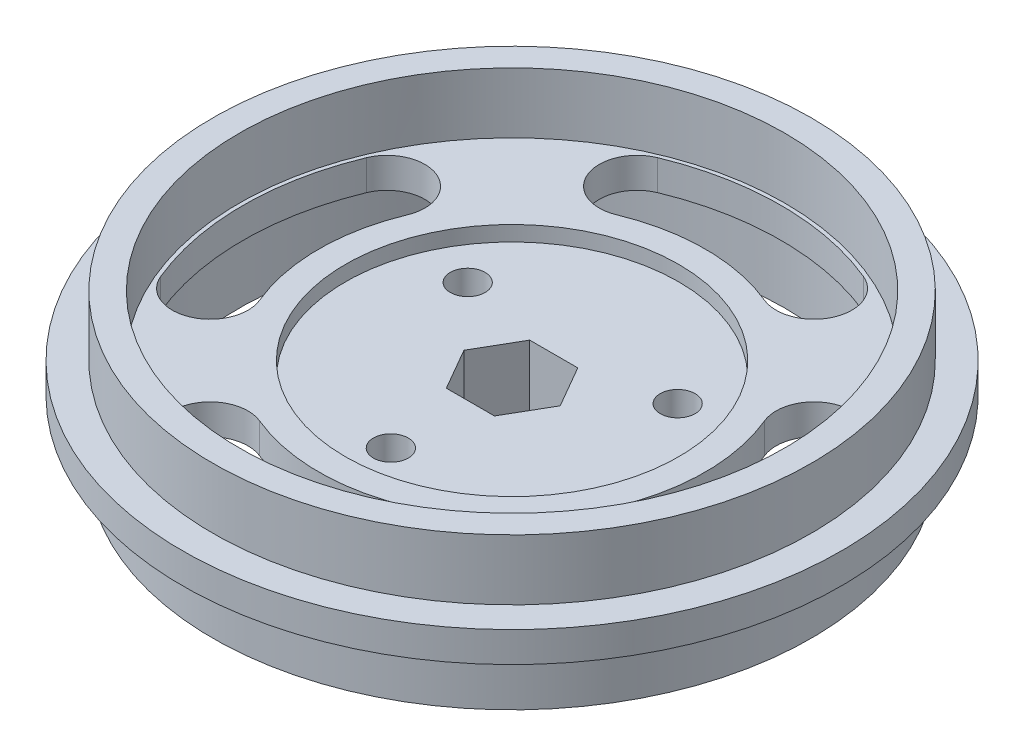
SolidWorks part; units mm, degrees
ref_plane "Ön Düzlem" through (0, 0, 0) normal (0, 0, 1) x (1, 0, 0)
ref_plane "Üst Düzlem" through (0, 0, 0) normal (0, 1, 0) x (1, 0, 0)
ref_plane "Sağ Düzlem" through (0, 0, 0) normal (1, 0, 0) x (0, 0, -1)
sketch "Sketch1" plane through (0, 0, 0) normal (0, 0, 1) x (1, 0, 0)
  line L0 (18, 5) -> (18, -5)
  line L1 (18, 5) -> (19.75, 5)
  line L2 (19.75, 5) -> (19.75, 1)
  line L3 (19.75, 1) -> (21.75, 1)
  line L4 (21.75, 1) -> (21.75, -1)
  line L5 (21.75, -1) -> (19.75, -1)
  line L6 (19.75, -1) -> (19.75, -5)
  line L7 (19.75, -5) -> (18, -5)
  line L8 (0, 0) -> (0, 50000) construction
  point P2 (18, 0)
  point P4 (21.75, 0)
  dimension "D1" = 18
  dimension "D2" = 10
  dimension "D3" = 2
  dimension "D4" = 4
  dimension "D5" = 1.75
  dimension "D6" = 2
revolve "Revolve1" add sketch "Sketch1" angle 360 about L8
ref_plane "Plane1" through (0, 0, 0) normal (0, 1, 0) x (1, 0, 0)
sketch "Sketch3" plane through (0, 0, 0) normal (0, 1, 0) x (1, 0, 0)
  line L0 (-6.7926, 16.3989) -> (0, 0) construction
  line L1 (0, 0) -> (6.7926, 16.3989) construction
  circle A0 centre (0, 0) radius 18
  circle A1 centre (0, 0) radius 18 construction
  arc A2 (-6.7926, 16.3989) -> (6.7926, 16.3989) centre (0, 0) cw
  arc A3 (4.8792, 11.7795) -> (-4.8792, 11.7795) centre (0, 0) ccw
  arc A4 (-6.7926, 16.3989) -> (-4.8792, 11.7795) centre (-5.8359, 14.0892) ccw
  arc A5 (4.8792, 11.7795) -> (6.7926, 16.3989) centre (5.8359, 14.0892) ccw
  arc A6 (11.7795, -4.8792) -> (11.7795, 4.8792) centre (0, 0) ccw
  arc A7 (11.7795, -4.8792) -> (16.3989, -6.7926) centre (14.0892, -5.8359) ccw
  arc A8 (16.3989, 6.7926) -> (11.7795, 4.8792) centre (14.0892, 5.8359) ccw
  arc A9 (16.3989, 6.7926) -> (16.3989, -6.7926) centre (0, 0) cw
  arc A10 (-4.8792, -11.7795) -> (4.8792, -11.7795) centre (0, 0) ccw
  arc A11 (-4.8792, -11.7795) -> (-6.7926, -16.3989) centre (-5.8359, -14.0892) ccw
  arc A12 (6.7926, -16.3989) -> (4.8792, -11.7795) centre (5.8359, -14.0892) ccw
  arc A13 (6.7926, -16.3989) -> (-6.7926, -16.3989) centre (0, 0) cw
  arc A14 (-11.7795, 4.8792) -> (-11.7795, -4.8792) centre (0, 0) ccw
  arc A15 (-11.7795, 4.8792) -> (-16.3989, 6.7926) centre (-14.0892, 5.8359) ccw
  arc A16 (-16.3989, -6.7926) -> (-11.7795, -4.8792) centre (-14.0892, -5.8359) ccw
  arc A17 (-16.3989, -6.7926) -> (-16.3989, 6.7926) centre (0, 0) cw
  point P7 (0, 17.75)
  point P37 (0, 0)
  dimension "D1" = 17.75
  dimension "D3" = 5
  dimension "D2" = 45
  dimension "D4" = 4
extrude "Boss-Extrude1" add sketch "Sketch3" along normal mid plane 2 contours A0 A5 A3 A4 A2 A8 A9 A7 A6 A12 A13 A11 A10 A16 A17 A15 A14
sketch "Sketch4" plane through (0, 1, 0) normal (0, 1, 0) x (1, 0, 0)
  circle A0 centre (0, 0) radius 11
  dimension "D1" = 22
extrude "Cut-Extrude1" cut sketch "Sketch4" against normal blind 1
sketch "Sketch5" plane through (0, 0, 0) normal (0, 1, 0) x (1, 0, 0)
  line L1 (3.1754, 0) -> (1.5877, 2.75)
  line L2 (1.5877, 2.75) -> (-1.5877, 2.75)
  line L3 (-1.5877, 2.75) -> (-3.1754, 0)
  line L4 (-3.1754, 0) -> (-1.5877, -2.75)
  line L5 (-1.5877, -2.75) -> (1.5877, -2.75)
  line L6 (1.5877, -2.75) -> (3.1754, 0)
  circle A0 centre (0, -8) radius 1.15
  circle A3 centre (-6.9282, 4) radius 1.15
  circle A4 centre (6.9282, 4) radius 1.15
  circle A7 centre (0, 0) radius 2.75 construction
  point P9 (0, 0)
  dimension "D1" = 2.3
  dimension "D3" = 8
  dimension "D4" = 5.5
  dimension "D2" = 3
extrude "Cut-Extrude2" cut sketch "Sketch5" against normal through all
sketch "Sketch6" plane through (0, -1, 0) normal (0, -1, 0) x (1, 0, 0)
  line L0 (3.1754, 0) -> (1.5877, -2.75) construction
  line L1 (1.5877, -2.75) -> (-1.5877, -2.75) construction
  line L2 (-1.5877, -2.75) -> (-3.1754, 0) construction
  line L3 (-3.1754, 0) -> (-1.5877, 2.75) construction
  line L4 (-1.5877, 2.75) -> (1.5877, 2.75) construction
  line L5 (1.5877, 2.75) -> (3.1754, 0) construction
  line L6 (3.1754, 0) -> (1.5877, -2.75)
  line L7 (1.5877, -2.75) -> (-1.5877, -2.75)
  line L8 (-1.5877, -2.75) -> (-3.1754, 0)
  line L9 (-3.1754, 0) -> (-1.5877, 2.75)
  line L10 (-1.5877, 2.75) -> (1.5877, 2.75)
  line L11 (1.5877, 2.75) -> (3.1754, 0)
  circle A0 centre (-6.9282, -4) radius 1.15 construction
  circle A1 centre (6.9282, -4) radius 1.15 construction
  circle A2 centre (0, 8) radius 1.15 construction
  circle A3 centre (0, 0) radius 11 construction
  circle A4 centre (-6.9282, -4) radius 1.15
  circle A5 centre (6.9282, -4) radius 1.15
  circle A6 centre (0, 8) radius 1.15
  circle A7 centre (0, 0) radius 11
extrude "Boss-Extrude2" add sketch "Sketch6" along normal blind 3
sketch "Sketch9" plane through (0, -4, 0) normal (0, -1, 0) x (1, 0, 0)
  line L0 (-1.5877, 2.75) -> (-3.1754, 0) construction
  line L1 (-3.1754, 0) -> (-1.5877, -2.75) construction
  line L2 (1.5877, 2.75) -> (-1.5877, 2.75) construction
  line L3 (3.1754, 0) -> (1.5877, 2.75) construction
  line L4 (1.5877, -2.75) -> (3.1754, 0) construction
  line L5 (-1.5877, -2.75) -> (1.5877, -2.75) construction
  line L6 (-1.5877, -2.75) -> (1.5877, -2.75)
  line L7 (1.5877, -2.75) -> (3.1754, 0)
  line L8 (3.1754, 0) -> (1.5877, 2.75)
  line L9 (1.5877, 2.75) -> (-1.5877, 2.75)
  line L10 (-3.1754, 0) -> (-1.5877, -2.75)
  line L11 (-1.5877, 2.75) -> (-3.1754, 0)
  circle A0 centre (0, 0) radius 11
  circle A1 centre (0, 0) radius 11 construction
  circle A2 centre (0, 8) radius 2.15
  circle A3 centre (-6.9282, -4) radius 2.15
  circle A4 centre (6.9282, -4) radius 2.15
  dimension "D1" = 4.3
extrude "Boss-Extrude3" add sketch "Sketch9" along normal blind 2
